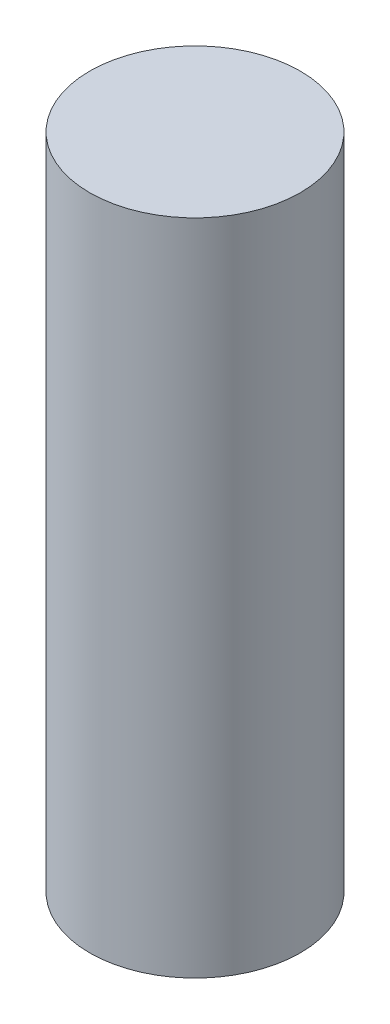
SolidWorks part; units mm, degrees
ref_plane "Front Plane" through (0, 0, 0) normal (0, 0, 1) x (1, 0, 0)
ref_plane "Top Plane" through (0, 0, 0) normal (0, 1, 0) x (1, 0, 0)
ref_plane "Right Plane" through (0, 0, 0) normal (1, 0, 0) x (0, 0, -1)
sketch "Sketch1" plane through (0, 0, 0) normal (0, 1, 0) x (1, 0, 0)
  circle A0 centre (0, 0) radius 4
extrude "Boss-Extrude1" add sketch "Sketch1" along normal blind 25
